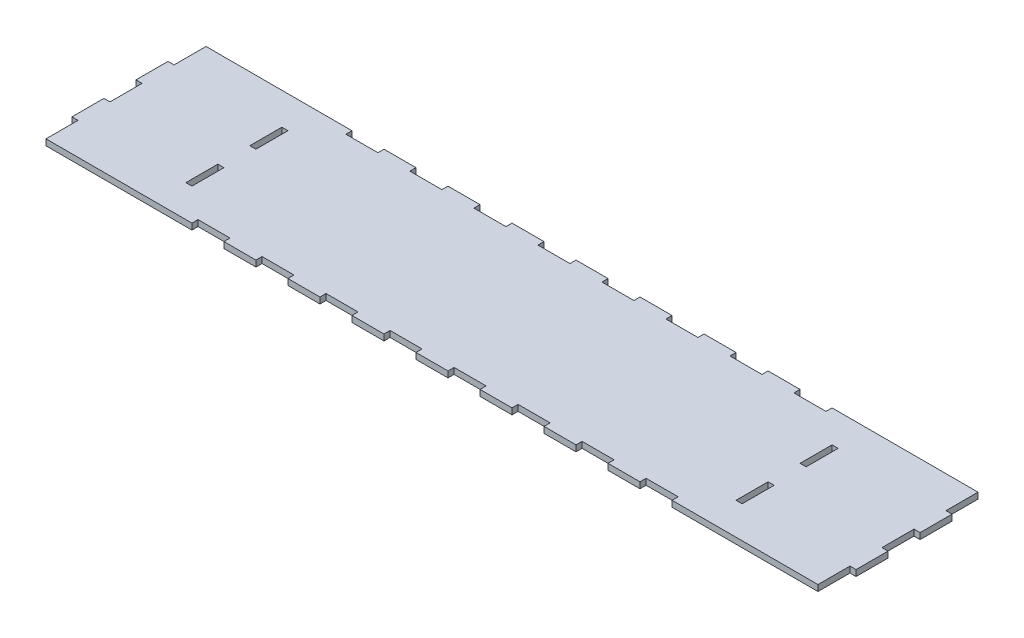
SolidWorks part; units mm, degrees
material "1060 Alloy"
ref_plane "Front Plane" through (0, 0, 0) normal (0, 0, 1) x (1, 0, 0)
ref_plane "Top Plane" through (0, 0, 0) normal (0, 1, 0) x (1, 0, 0)
ref_plane "Right Plane" through (0, 0, 0) normal (1, 0, 0) x (0, 0, -1)
sketch "Sketch1" plane through (0, 0, 0) normal (0, 1, 0) x (1, 0, 0)
  line L0 (0, 101.6) -> (0, 127)
  line L1 (0, 0) -> (612.648, 0)
  line L2 (0, 0) -> (0, 25.4)
  line L3 (0, 127) -> (612.648, 127)
  line L4 (612.648, 0) -> (612.648, 25.4)
  line L5 (0, 101.6) -> (-4.826, 101.6)
  line L7 (0, 76.2) -> (-4.826, 76.2)
  line L8 (-4.826, 101.6) -> (-4.826, 76.2)
  line L9 (0, 50.8) -> (-4.826, 50.8)
  line L11 (0, 25.4) -> (-4.826, 25.4)
  line L12 (-4.826, 50.8) -> (-4.826, 25.4)
  line L13 (612.648, 101.6) -> (617.474, 101.6)
  line L15 (612.648, 76.2) -> (617.474, 76.2)
  line L16 (617.474, 101.6) -> (617.474, 76.2)
  line L17 (612.648, 50.8) -> (617.474, 50.8)
  line L19 (612.648, 25.4) -> (617.474, 25.4)
  line L20 (617.474, 50.8) -> (617.474, 25.4)
  line L21 (0, 50.8) -> (0, 76.2)
  line L22 (612.648, 50.8) -> (612.648, 76.2)
  line L23 (612.648, 101.6) -> (612.648, 127)
  dimension "D1" = 622.3
  dimension "D2" = 127
  dimension "D3" = 4.826
extrude "Boss-Extrude1" add sketch "Sketch1" along normal blind 4.826 contours L3 L23 L13 L16 L15 L22 L17 L20 L19 L4 L1 L2 L11 L12 L9 L21 L7 L8 L5 L0
sketch "Sketch2" plane through (0, 4.826, 0) normal (0, 1, 0) x (1, 0, 0)
  line L1 (522.224, 101.6) -> (527.05, 101.6)
  line L2 (522.224, 101.6) -> (522.224, 76.2)
  line L3 (522.224, 76.2) -> (527.05, 76.2)
  line L4 (527.05, 101.6) -> (527.05, 76.2)
  line L5 (522.224, 50.8) -> (527.05, 50.8)
  line L6 (522.224, 50.8) -> (522.224, 25.4)
  line L7 (522.224, 25.4) -> (527.05, 25.4)
  line L8 (527.05, 50.8) -> (527.05, 25.4)
  line L10 (612.648, 50.8) -> (617.474, 50.8) construction
  line L11 (612.648, 25.4) -> (617.474, 25.4) construction
  line L12 (612.648, 76.2) -> (617.474, 76.2) construction
  line L13 (612.648, 101.6) -> (617.474, 101.6) construction
  line L14 (617.474, 50.8) -> (617.474, 25.4) construction
  line L15 (306.324, 127) -> (306.324, 0) construction
  line L16 (0, 127) -> (612.648, 127) construction
  line L17 (0, 0) -> (612.648, 0) construction
  line L18 (85.598, 50.8) -> (85.598, 25.4)
  line L19 (90.424, 25.4) -> (85.598, 25.4)
  line L20 (90.424, 50.8) -> (90.424, 25.4)
  line L21 (90.424, 50.8) -> (85.598, 50.8)
  line L22 (85.598, 101.6) -> (85.598, 76.2)
  line L23 (90.424, 76.2) -> (85.598, 76.2)
  line L24 (90.424, 101.6) -> (90.424, 76.2)
  line L25 (90.424, 101.6) -> (85.598, 101.6)
  dimension "D1" = 95.25
extrude "Cut-Extrude1" cut sketch "Sketch2" against normal through all
sketch "Sketch3" plane through (0, 4.826, 0) normal (0, 1, 0) x (1, 0, 0)
  line L0 (471.424, 127) -> (446.024, 127)
  line L1 (496.824, 122.174) -> (471.424, 122.174)
  line L2 (496.824, 122.174) -> (496.824, 127)
  line L3 (217.424, 127) -> (192.024, 127)
  line L4 (471.424, 122.174) -> (471.424, 127)
  line L5 (446.024, 122.174) -> (420.624, 122.174)
  line L6 (446.024, 122.174) -> (446.024, 127)
  line L7 (166.624, 127) -> (141.224, 127)
  line L8 (420.624, 122.174) -> (420.624, 127)
  line L9 (395.224, 122.174) -> (369.824, 122.174)
  line L10 (395.224, 122.174) -> (395.224, 127)
  line L11 (115.824, 127) -> (90.424, 127)
  line L12 (369.824, 122.174) -> (369.824, 127)
  line L13 (344.424, 122.174) -> (319.024, 122.174)
  line L14 (344.424, 122.174) -> (344.424, 127)
  line L15 (522.224, 101.6) -> (522.224, 127)
  line L16 (319.024, 122.174) -> (319.024, 127)
  line L17 (293.624, 122.174) -> (268.224, 122.174)
  line L18 (293.624, 122.174) -> (293.624, 127)
  line L19 (90.424, 101.6) -> (90.424, 127)
  line L20 (0, 127) -> (0, 101.6)
  line L21 (0, 101.6) -> (-4.826, 101.6)
  line L22 (-4.826, 101.6) -> (-4.826, 76.2)
  line L23 (-4.826, 76.2) -> (0, 76.2)
  line L24 (0, 76.2) -> (0, 50.8)
  line L25 (0, 50.8) -> (-4.826, 50.8)
  line L26 (-4.826, 50.8) -> (-4.826, 25.4)
  line L27 (-4.826, 25.4) -> (0, 25.4)
  line L28 (0, 25.4) -> (0, 0)
  line L29 (0, 0) -> (612.648, 0)
  line L30 (612.648, 0) -> (612.648, 25.4)
  line L31 (612.648, 25.4) -> (617.474, 25.4)
  line L32 (617.474, 25.4) -> (617.474, 50.8)
  line L33 (617.474, 50.8) -> (612.648, 50.8)
  line L34 (612.648, 50.8) -> (612.648, 76.2)
  line L35 (612.648, 76.2) -> (617.474, 76.2)
  line L36 (617.474, 76.2) -> (617.474, 101.6)
  line L37 (617.474, 101.6) -> (612.648, 101.6)
  line L38 (612.648, 101.6) -> (612.648, 127)
  line L39 (612.648, 127) -> (0, 127)
  line L40 (0, 127) -> (0, 101.6)
  line L41 (0, 101.6) -> (-4.826, 101.6)
  line L42 (-4.826, 101.6) -> (-4.826, 76.2)
  line L43 (-4.826, 76.2) -> (0, 76.2)
  line L44 (0, 76.2) -> (0, 50.8)
  line L45 (0, 50.8) -> (-4.826, 50.8)
  line L46 (-4.826, 50.8) -> (-4.826, 25.4)
  line L47 (-4.826, 25.4) -> (0, 25.4)
  line L48 (0, 25.4) -> (0, 0)
  line L49 (0, 0) -> (612.648, 0)
  line L50 (612.648, 0) -> (612.648, 25.4)
  line L51 (612.648, 25.4) -> (617.474, 25.4)
  line L52 (617.474, 25.4) -> (617.474, 50.8)
  line L53 (617.474, 50.8) -> (612.648, 50.8)
  line L54 (612.648, 50.8) -> (612.648, 76.2)
  line L55 (612.648, 76.2) -> (617.474, 76.2)
  line L56 (617.474, 76.2) -> (617.474, 101.6)
  line L57 (617.474, 101.6) -> (612.648, 101.6)
  line L58 (612.648, 101.6) -> (612.648, 127)
  line L59 (522.224, 127) -> (496.824, 127)
  line L60 (268.224, 122.174) -> (268.224, 127)
  line L61 (242.824, 122.174) -> (217.424, 122.174)
  line L62 (242.824, 122.174) -> (242.824, 127)
  line L63 (612.648, 63.5) -> (0, 63.5) construction
  line L64 (217.424, 122.174) -> (217.424, 127)
  line L65 (192.024, 122.174) -> (166.624, 122.174)
  line L66 (192.024, 122.174) -> (192.024, 127)
  line L67 (268.224, 0) -> (242.824, 0)
  line L68 (166.624, 122.174) -> (166.624, 127)
  line L69 (141.224, 122.174) -> (115.824, 122.174)
  line L70 (141.224, 122.174) -> (141.224, 127)
  line L71 (319.024, 0) -> (293.624, 0)
  line L72 (115.824, 122.174) -> (115.824, 127)
  line L73 (420.624, 127) -> (395.224, 127)
  line L74 (369.824, 127) -> (344.424, 127)
  line L75 (319.024, 127) -> (293.624, 127)
  line L76 (268.224, 127) -> (242.824, 127)
  line L77 (369.824, 0) -> (344.424, 0)
  line L78 (420.624, 0) -> (395.224, 0)
  line L79 (115.824, 4.826) -> (115.824, 0)
  line L80 (522.224, 101.6) -> (522.224, 76.2) construction
  line L81 (90.424, 76.2) -> (90.424, 101.6) construction
  line L82 (522.224, 101.6) -> (522.224, 76.2)
  line L83 (90.424, 76.2) -> (90.424, 101.6)
  line L84 (141.224, 4.826) -> (141.224, 0)
  line L85 (141.224, 4.826) -> (115.824, 4.826)
  line L86 (166.624, 4.826) -> (166.624, 0)
  line L87 (192.024, 4.826) -> (192.024, 0)
  line L88 (192.024, 4.826) -> (166.624, 4.826)
  line L89 (217.424, 4.826) -> (217.424, 0)
  line L90 (242.824, 4.826) -> (242.824, 0)
  line L91 (242.824, 4.826) -> (217.424, 4.826)
  line L92 (268.224, 4.826) -> (268.224, 0)
  line L93 (522.224, 0) -> (496.824, 0)
  line L94 (612.648, 25.4) -> (612.648, 0)
  line L95 (617.474, 25.4) -> (612.648, 25.4)
  line L96 (90.424, 25.4) -> (90.424, 0)
  line L97 (293.624, 4.826) -> (293.624, 0)
  line L98 (293.624, 4.826) -> (268.224, 4.826)
  line L99 (319.024, 4.826) -> (319.024, 0)
  line L100 (522.224, 25.4) -> (522.224, 0)
  line L101 (344.424, 4.826) -> (344.424, 0)
  line L102 (344.424, 4.826) -> (319.024, 4.826)
  line L103 (369.824, 4.826) -> (369.824, 0)
  line L104 (115.824, 0) -> (90.424, 0)
  line L105 (395.224, 4.826) -> (395.224, 0)
  line L106 (395.224, 4.826) -> (369.824, 4.826)
  line L107 (420.624, 4.826) -> (420.624, 0)
  line L108 (166.624, 0) -> (141.224, 0)
  line L109 (446.024, 4.826) -> (446.024, 0)
  line L110 (446.024, 4.826) -> (420.624, 4.826)
  line L111 (471.424, 4.826) -> (471.424, 0)
  line L112 (217.424, 0) -> (192.024, 0)
  line L113 (496.824, 4.826) -> (496.824, 0)
  line L114 (496.824, 4.826) -> (471.424, 4.826)
  line L115 (471.424, 0) -> (446.024, 0)
  line M67 (0, 0) -> (612.648, 0)
  line M77 (612.648, 127) -> (0, 127)
  dimension "D2" = 4.826
extrude "Cut-Extrude2" cut sketch "Sketch3" against normal through all contours L113 L114 L111 M67 | L109 L110 L107 M67 | L105 L106 L103 M67 | L101 L102 L99 M67 | L97 L98 L92 M67 | L90 L91 L89 L49 | L84 L85 L79 L49 | L87 L88 L86 L49 | L72 L69 L70 M77 | L68 L65 L66 M77 | L64 L61 L62 M77 | L60 L17 L18 M77 | L16 L13 L14 M77 | L12 L9 L10 M77 | L8 L5 L6 M77 | L4 L1 L2 M77
equation "\"w\"= .19"
equation "\"D3@Sketch1\"=\"w\""
equation "\"D1@Boss-Extrude1\"=\"w\""
equation "\"D2@Sketch3\"=\"w\""
